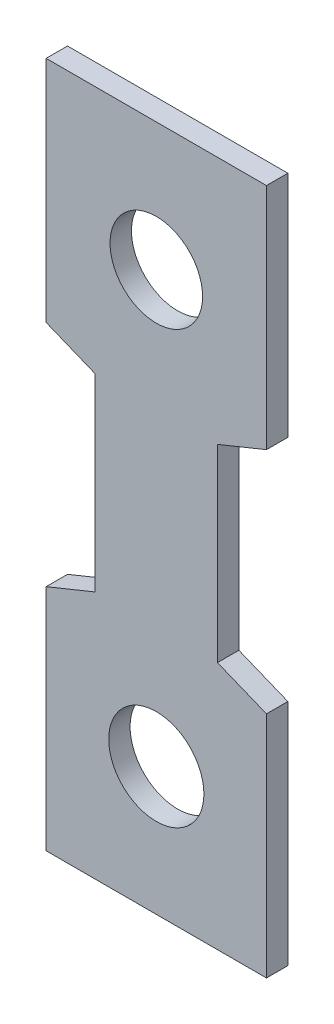
SolidWorks part; units mm, degrees
material "Copper"
ref_plane "Front Plane" through (0, 0, 0) normal (0, 0, 1) x (1, 0, 0)
ref_plane "Top Plane" through (0, 0, 0) normal (0, 1, 0) x (1, 0, 0)
ref_plane "Right Plane" through (0, 0, 0) normal (1, 0, 0) x (0, 0, -1)
sketch "Sketch1" plane through (0, 0, 0) normal (0, 0, 1) x (1, 0, 0)
  line L0 (-5.6261, 28.5115) -> (5.6261, 28.5115)
  line L1 (5.6261, 28.5115) -> (5.6261, 16.8275)
  line L2 (5.6261, 16.8275) -> (3.1242, 15.8115)
  line L3 (3.1242, 15.8115) -> (3.1242, 6.1595)
  line L4 (3.1242, 6.1595) -> (5.6261, 5.1435)
  line L5 (5.6261, 5.1435) -> (5.6261, -6.5405)
  line L6 (5.6261, -6.5405) -> (-5.6261, -6.5405)
  line L7 (-5.6261, -6.5405) -> (-5.6261, 5.1435)
  line L8 (-5.6261, 5.1435) -> (-3.1242, 6.1595)
  line L9 (-3.1242, 6.1595) -> (-3.1242, 15.8115)
  line L10 (-3.1242, 15.8115) -> (-5.6261, 16.8275)
  line L11 (-5.6261, 16.8275) -> (-5.6261, 28.5115)
  line L13 (0, 21.971) -> (0, 0) construction
  circle A0 centre (0, 0) radius 2.4309
  circle A1 centre (0, 21.971) radius 2.363
  point P7 (0, 10.9855)
  point P18 (3.1242, 10.9855)
  dimension "D1" = 21.971
  dimension "D2" = 6.2484
  dimension "D3" = 11.2522
  dimension "D4" = 1.016
  dimension "D5" = 35.052
  dimension "D6" = 11.684
extrude "Boss-Extrude1" add sketch "Sketch1" along normal blind 1.0922
